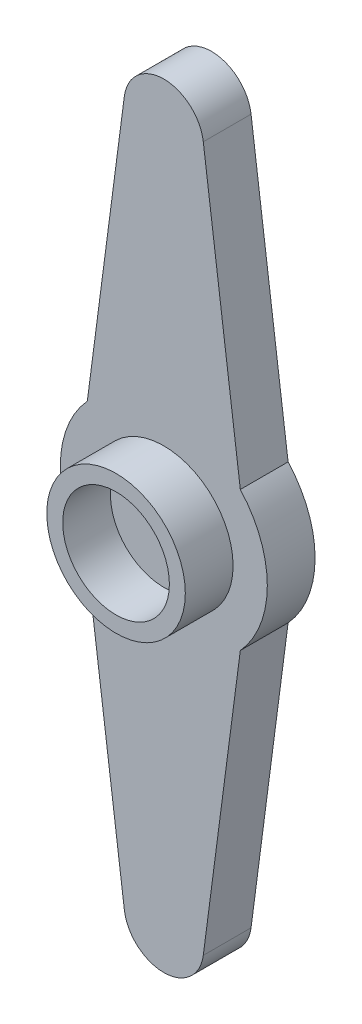
SolidWorks part; units mm, degrees
ref_plane "前视基准面" through (0, 0, 0) normal (0, 0, 1) x (1, 0, 0)
ref_plane "上视基准面" through (0, 0, 0) normal (0, 1, 0) x (1, 0, 0)
ref_plane "右视基准面" through (0, 0, 0) normal (1, 0, 0) x (0, 0, -1)
sketch "草图1" plane through (0, 0, 0) normal (0, 0, 1) x (1, 0, 0)
  line L0 (-2.4788, 22.1249) -> (-4.8048, 4.3776)
  line L1 (0, 29.2442) -> (0, -1.8273) construction
  line L2 (2.4788, 22.1249) -> (4.8048, 4.3776)
  line L3 (2.4788, -22.1249) -> (4.8048, -4.3776)
  line L4 (-2.4788, -22.1249) -> (-4.8048, -4.3776)
  line L5 (0, -29.2442) -> (0, -24.3) construction
  line L6 (0, -1.8273) -> (0, 1.8273) construction
  arc A0 (-4.8048, 4.3776) -> (-4.8048, -4.3776) centre (0, 0) ccw
  arc A1 (2.4788, 22.1249) -> (-2.4788, 22.1249) centre (0, 21.8) ccw
  arc A2 (-2.4788, -22.1249) -> (2.4788, -22.1249) centre (0, -21.8) ccw
  arc A3 (4.8048, -4.3776) -> (4.8048, 4.3776) centre (0, 0) ccw
  point P18 (0, 0)
  dimension "D1" = 13
  dimension "D2" = 5
  dimension "D3" = 21.8
  dimension "D4" = 2
extrude "凸台-拉伸1" add sketch "草图1" along normal blind 3
sketch "草图2" plane through (0, 0, 3) normal (0, 0, 1) x (1, 0, 0)
  circle A0 centre (0, 0) radius 4.35
extrude "拉伸-薄壁1" add sketch "草图2" along normal offset from surface (3 mm away) 6 thin up to face at (0, 0, 0) thin type one direction reverse wall 1
